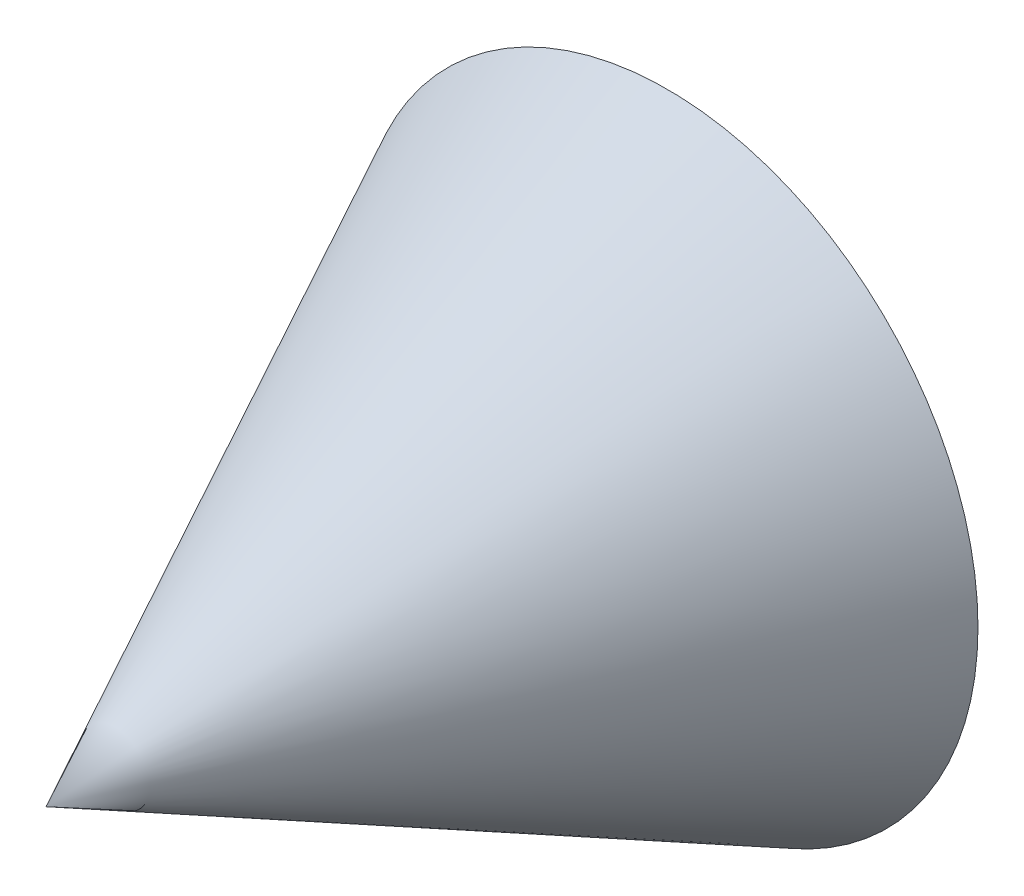
SolidWorks part; units mm, degrees
ref_plane "Plano frontal" through (0, 0, 0) normal (0, 0, 1) x (1, 0, 0)
ref_plane "Plano superior" through (0, 0, 0) normal (0, 1, 0) x (1, 0, 0)
ref_plane "Plano direito" through (0, 0, 0) normal (1, 0, 0) x (0, 0, -1)
ref_plane "Plano1" through (0, 0, 100) normal (0, 0, 1) x (1, 0, 0)
sketch "Esboço1" plane through (0, 0, 0) normal (0, 0, 1) x (1, 0, 0)
  circle A0 centre (0, 0) radius 50
  dimension "D1" = 100
sketch "Esboço2" plane through (0, 0, 100) normal (0, 0, 1) x (1, 0, 0)
  point P0 (0, 0)
loft "Loft1" add profiles "Esboço1", "Esboço2"
